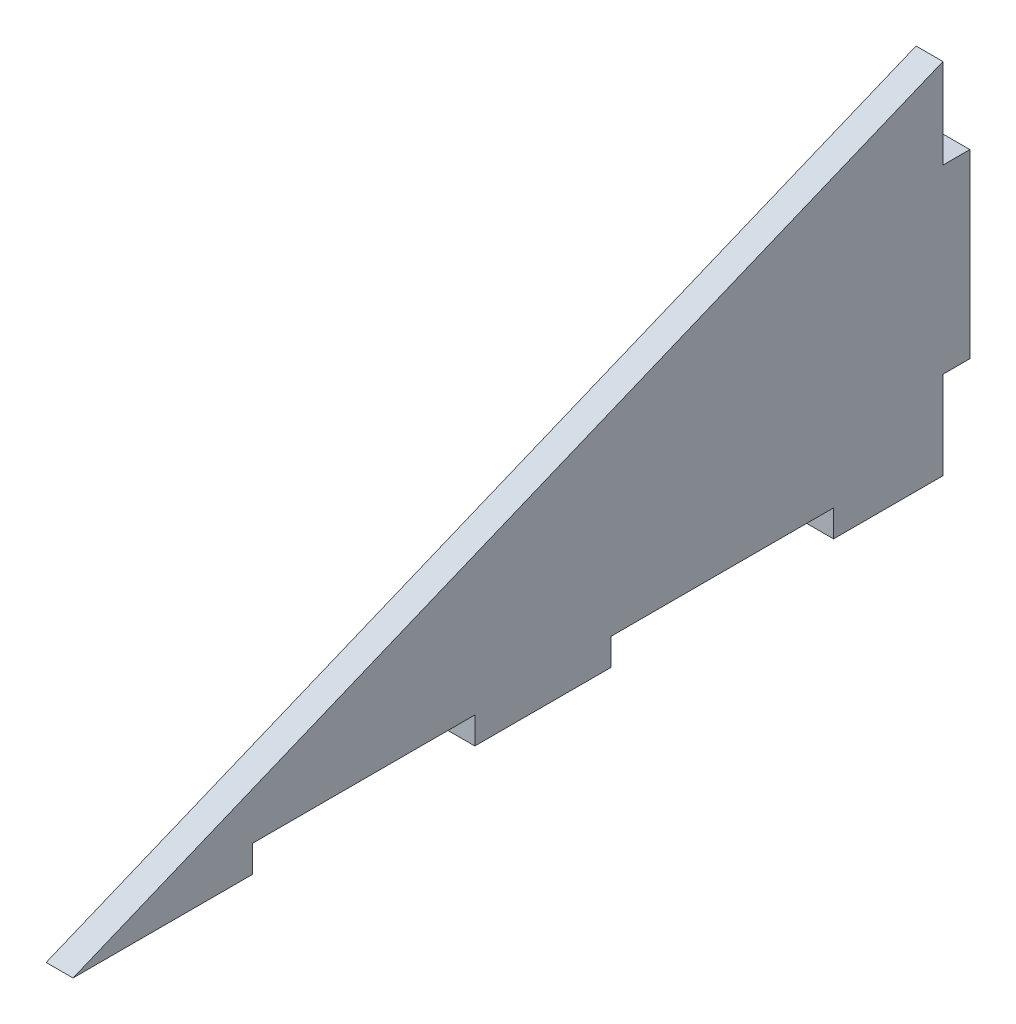
SolidWorks part; units mm, degrees
ref_plane "Front Plane" through (0, 0, 0) normal (0, 0, 1) x (1, 0, 0)
ref_plane "Top Plane" through (0, 0, 0) normal (0, 1, 0) x (1, 0, 0)
ref_plane "Right Plane" through (0, 0, 0) normal (1, 0, 0) x (0, 0, -1)
sketch "Sketch1" plane through (0, 0, 0) normal (1, 0, 0) x (0, 0, -1)
  line L1 (-3, 30) -> (0, 30)
  line L2 (0, 55) -> (0, -55) construction
  line L3 (0, 30) -> (0, 9.8)
  line L4 (0, 9.8) -> (-3, 9.8)
  line L5 (-3, 9.8) -> (-3, 0)
  line L6 (55, 0) -> (-55, 0) construction
  line L7 (-3, 0) -> (-100, 0)
  line L9 (-100, 0) -> (-3, 40)
  line L10 (-3, 40) -> (-3, 30)
  line L11 (-40, 0) -> (-40, 3)
  line L12 (-80, 0) -> (-55.2, 0)
  line L13 (-80, 0) -> (-80, 3)
  line L14 (-80, 3) -> (-55.2, 3)
  line L15 (-55.2, 0) -> (-55.2, 3)
  line L16 (-40, 0) -> (-15.2, 0)
  line L17 (-15.2, 0) -> (-15.2, 3)
  line L18 (-40, 3) -> (-15.2, 3)
  dimension "D1" = 9.8
  dimension "D2" = 3
  dimension "D3" = 20.2
  dimension "D4" = 100
  dimension "D5" = 40
  dimension "D6" = 3
  dimension "D7" = 24.8
  dimension "D8" = 3
  dimension "D9" = 20
  dimension "D11" = 15.2
  dimension "D10" = 2
extrude "Boss-Extrude1" add sketch "Sketch1" along normal blind 3 contours L11 L18 L17 L7 L5 L4 L3 L1 L10 L9 L13 L14 L15
